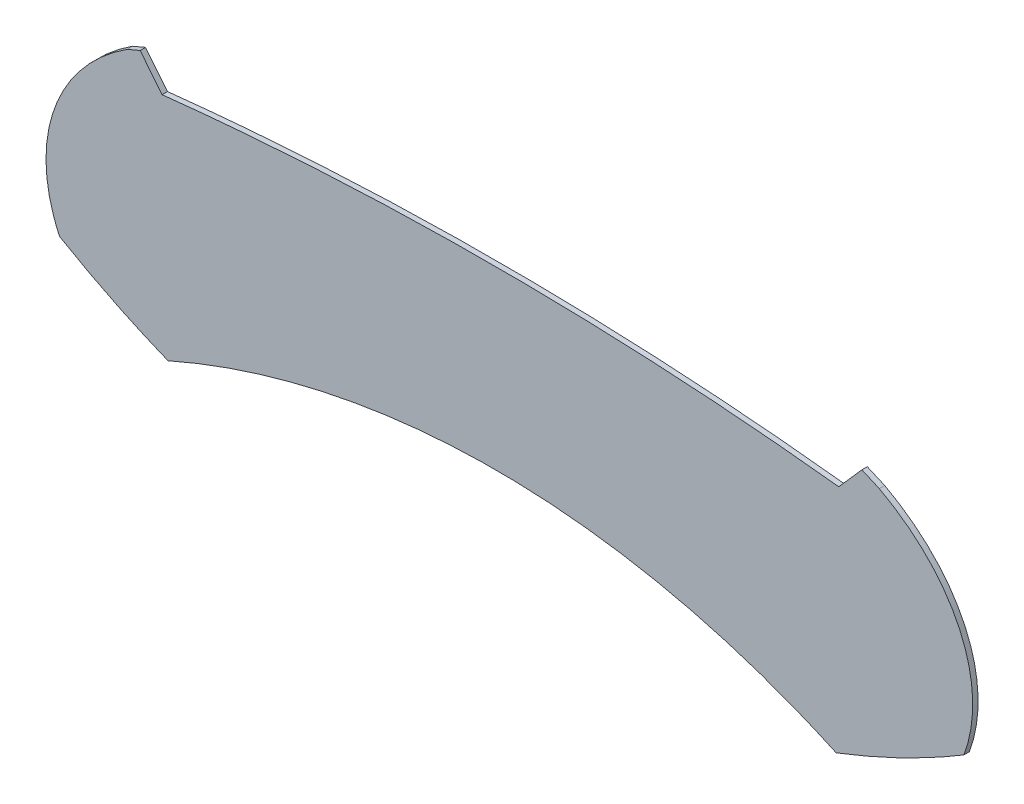
SolidWorks part; units mm, degrees
ref_plane "Alzado" through (0, 0, 0) normal (0, 0, 1) x (1, 0, 0)
ref_plane "Planta" through (0, 0, 0) normal (0, 1, 0) x (1, 0, 0)
ref_plane "Vista lateral" through (0, 0, 0) normal (1, 0, 0) x (0, 0, -1)
sketch "Model" plane through (0, 0, 0) normal (0, 0, 1) x (1, 0, 0)
  spline S0 degree 2 poles (54.5706, 30.8095) (54.3675, 31.0623) (54.1644, 31.3152) knots 5.050094 5.050094 5.050094 6.050094 6.050094 6.050094 weights 1 1 1
  spline S1 degree 2 poles (67.0989, 30.7871) (60.8367, 31.4894) (54.5706, 30.8095) knots 4.776004 4.776004 4.776004 5.050094 5.050094 5.050094 weights 1 0.990624 1
  spline S2 degree 2 poles (67.5275, 31.2729) (67.3132, 31.03) (67.0989, 30.7871) knots 3.776004 3.776004 3.776004 4.776004 4.776004 4.776004 weights 1 1 1
  spline S3 degree 2 poles (67.8498, 31.133) (67.6897, 31.2046) (67.5275, 31.2729) knots 3.75062 3.75062 3.75062 3.776004 3.776004 3.776004 weights 1 0.999919 1
  spline S4 degree 2 poles (69.4169, 27.6461) (70.2361, 29.8506) (67.8498, 31.133) knots 2.482364 2.482364 2.482364 3.75062 3.75062 3.75062 weights 1 0.805589 1
  spline S5 degree 2 poles (67.0514, 26.4965) (68.3055, 26.9774) (69.4169, 27.6461) knots 2.284513 2.284513 2.284513 2.482364 2.482364 2.482364 weights 1 0.995111 1
  spline S6 degree 2 poles (54.6801, 26.5981) (60.8888, 29.3455) (67.0514, 26.4965) knots 1.434861 1.434861 1.434861 2.284513 2.284513 2.284513 weights 1 0.91111 1
  spline S7 degree 2 poles (52.6705, 27.5878) (53.623, 27.025) (54.6801, 26.5981) knots 1.266243 1.266243 1.266243 1.434861 1.434861 1.434861 weights 1 0.996448 1
  spline S8 degree 2 poles (53.9245, 31.2137) (51.6669, 29.7617) (52.6705, 27.5878) knots 0.018792 0.018792 0.018792 1.266243 1.266243 1.266243 weights 1 0.811708 1
  spline S9 degree 2 poles (54.1644, 31.3152) (54.0439, 31.2653) (53.9245, 31.2137) knots 0 0 0 0.018792 0.018792 0.018792 weights 1 0.999956 1
extrude "Saliente-Extruir1" add sketch "Model" along normal blind 0.1
